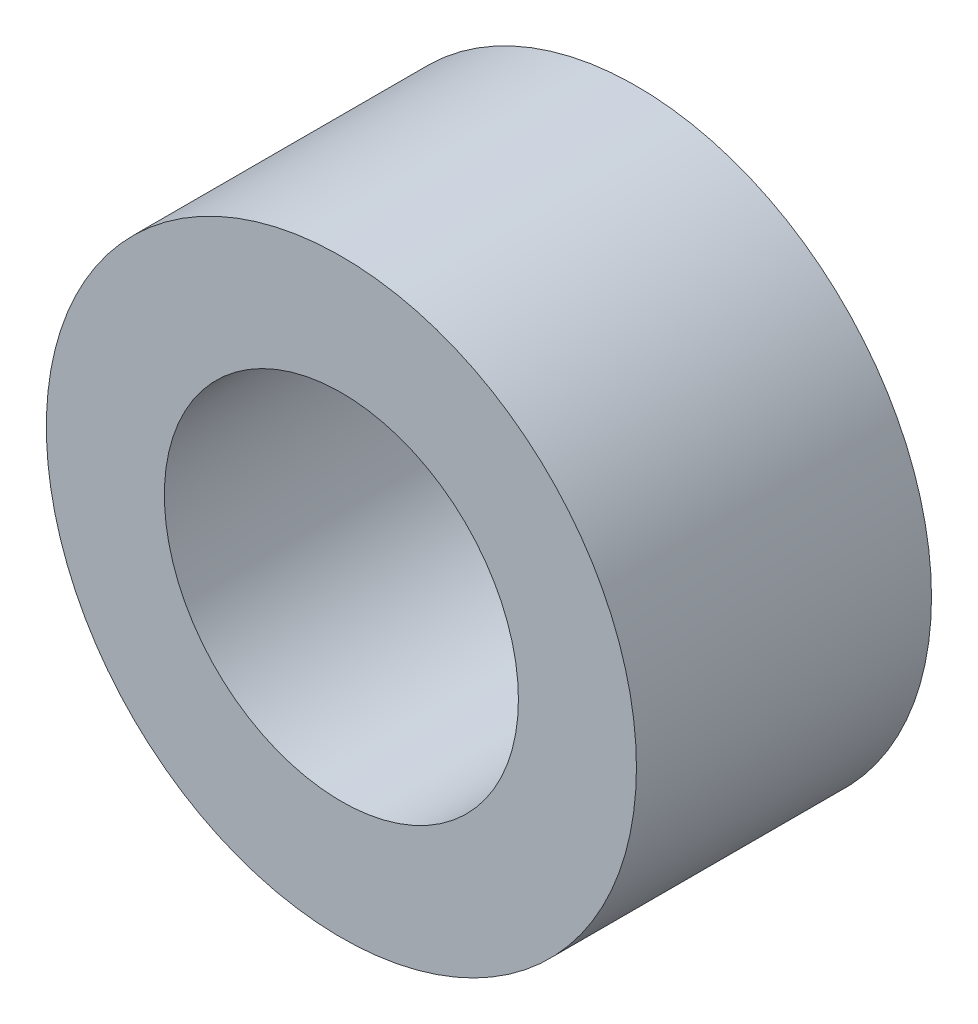
SolidWorks part; units mm, degrees
ref_plane "Front Plane" through (0, 0, 0) normal (0, 0, 1) x (1, 0, 0)
ref_plane "Top Plane" through (0, 0, 0) normal (0, 1, 0) x (1, 0, 0)
ref_plane "Right Plane" through (0, 0, 0) normal (1, 0, 0) x (0, 0, -1)
sketch "Croquis1" plane through (0, 0, 0) normal (0, 0, 1) x (1, 0, 0)
  circle A0 centre (0, 0) radius 3
  circle A1 centre (0, 0) radius 5
  dimension "D1" = 10
  dimension "D2" = 6
extrude "Saliente-Extruir1" add sketch "Croquis1" along normal blind 5
